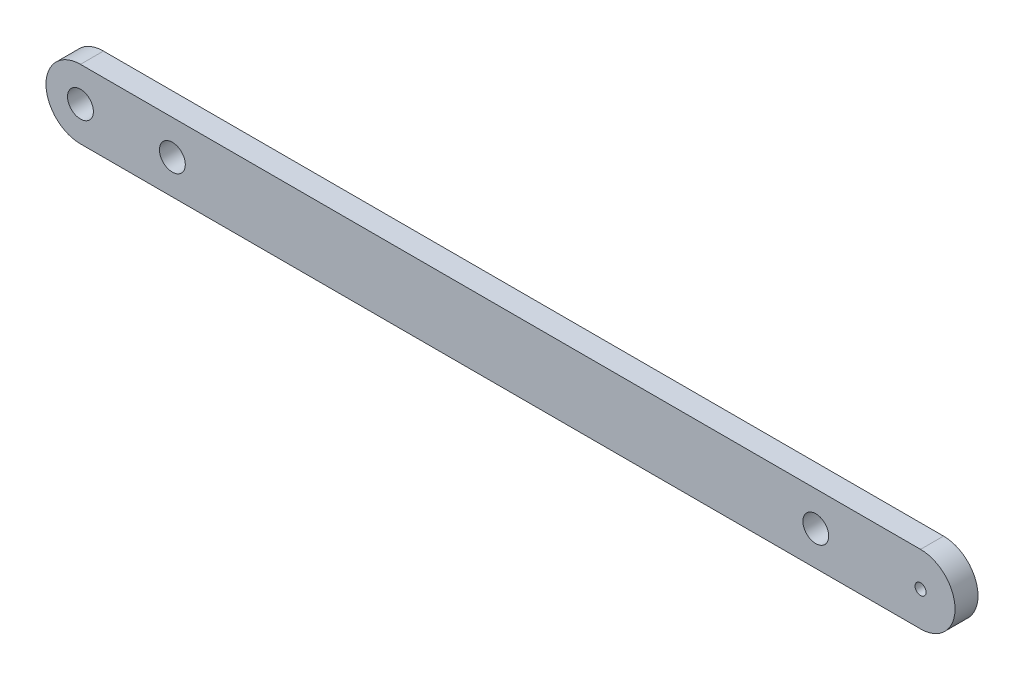
SolidWorks part; units mm, degrees
ref_plane "Front Plane" through (0, 0, 0) normal (0, 0, 1) x (1, 0, 0)
ref_plane "Top Plane" through (0, 0, 0) normal (0, 1, 0) x (1, 0, 0)
ref_plane "Right Plane" through (0, 0, 0) normal (1, 0, 0) x (0, 0, -1)
sketch "Sketch1" plane through (0, 0, 0) normal (0, 0, 1) x (1, 0, 0)
  line L0 (-6.1595, 0) -> (-127, 0) construction
  line L1 (-10.922, -4.7625) -> (-127, -4.7625)
  line L2 (-25.4, 4.7625) -> (-127, 4.7625)
  line L5 (-25.4, 4.7625) -> (-10.922, 4.7625)
  arc A1 (-127, 4.7625) -> (-127, -4.7625) centre (-127, 0) ccw
  circle A2 centre (-25.4, 0) radius 0.762
  circle A3 centre (-10.922, 0) radius 0.762
  arc A4 (-10.922, -4.7625) -> (-10.922, 4.7625) centre (-10.922, 0) ccw
  point P3 (-63.5, 0)
  dimension "D1" = 9.525
  dimension "D3" = 1.524
  dimension "D2" = 101.6
  dimension "D4" = 14.478
extrude "Boss-Extrude1" add sketch "Sketch1" along normal blind 3.175
hole_wizard "9/64 (0.14063) Diameter Hole1" positions "Sketch3" profile "Sketch2" hole size "9/64" standard "ANSI Inch" end condition through all
sketch "Sketch3" plane through (0, 0, 3.175) normal (0, 0, 1) x (1, 0, 0)
  point P0 (0, 0)
  point P3 (-127, 0)
sketch "Sketch2" plane through (0, 0, 3.175) normal (1, 0, 0) x (0, -1, 0)
  line L0 (0, 0) -> (0, 3.175)
  line L1 (0, 3.175) -> (1.786, 3.175)
  line L2 (1.786, 3.175) -> (1.786, 0)
  line L5 (1.786, 0) -> (0, 0)
  line L11 (0, -6.35) -> (0, 107.95) construction
  dimension "Thru Hole Dia." = 3.572
  dimension "Thru Hole Depth" = 3.175
hole_wizard "9/64 (0.14063) Diameter Hole2" positions "Sketch5" profile "Sketch4" hole size "9/64" standard "ANSI Inch" end condition through all
sketch "Sketch5" plane through (0, 0, 3.175) normal (0, 0, 1) x (1, 0, 0)
  circle A0 centre (-127, 0) radius 1.786 construction
  point P0 (-114.3, 0)
  dimension "D1" = 12.7
sketch "Sketch4" plane through (-114.3, 0, 3.175) normal (1, 0, 0) x (0, -1, 0)
  line L0 (0, 0) -> (0, 3.175)
  line L1 (0, 3.175) -> (1.786, 3.175)
  line L2 (1.786, 3.175) -> (1.786, 0)
  line L5 (1.786, 0) -> (0, 0)
  line L11 (0, -6.35) -> (0, 107.95) construction
  dimension "Thru Hole Dia." = 3.572
  dimension "Thru Hole Depth" = 3.175
hole_wizard "9/64 (0.14063) Diameter Hole3" positions "Sketch7" profile "Sketch6" hole size "9/64" standard "ANSI Inch" end condition through all
sketch "Sketch7" plane through (0, 0, 3.175) normal (0, 0, 1) x (1, 0, 0)
  circle A0 centre (-127, 0) radius 1.786 construction
  point P0 (-25.4, 0)
  dimension "D1" = 101.6
sketch "Sketch6" plane through (-25.4, 0, 3.175) normal (1, 0, 0) x (0, -1, 0)
  line L0 (0, 0) -> (0, 3.175)
  line L1 (0, 3.175) -> (1.786, 3.175)
  line L2 (1.786, 3.175) -> (1.786, 0)
  line L5 (1.786, 0) -> (0, 0)
  line L11 (0, -6.35) -> (0, 107.95) construction
  dimension "Thru Hole Dia." = 3.572
  dimension "Thru Hole Depth" = 3.175
